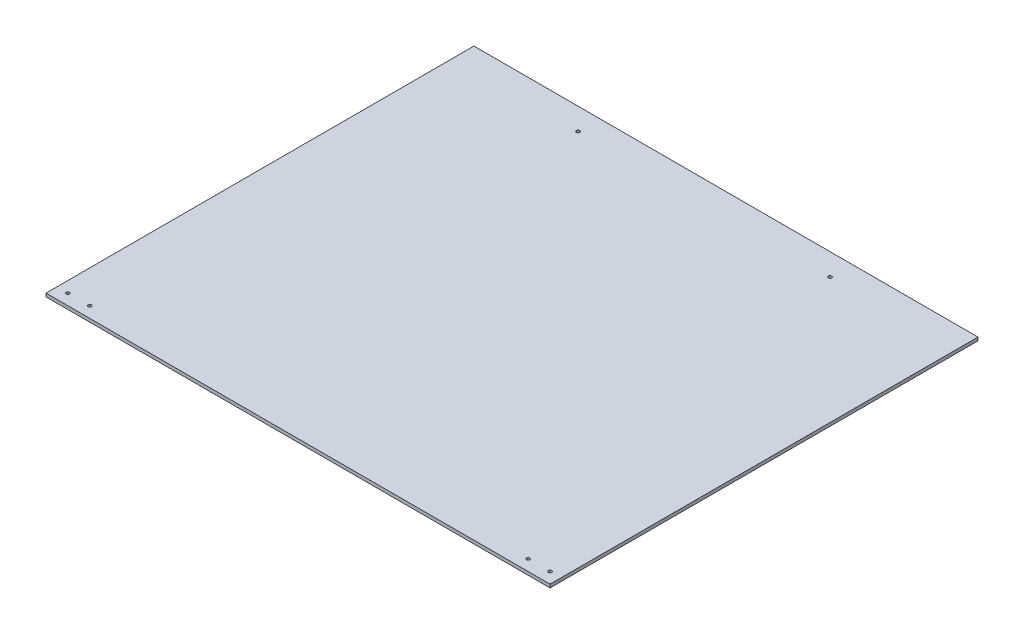
SolidWorks part; units mm, degrees
ref_plane "Front Plane" through (0, 0, 0) normal (0, 0, 1) x (1, 0, 0)
ref_plane "Top Plane" through (0, 0, 0) normal (0, 1, 0) x (1, 0, 0)
ref_plane "Right Plane" through (0, 0, 0) normal (1, 0, 0) x (0, 0, -1)
sketch "Sketch3" plane through (0, 0, 0) normal (0, 1, 0) x (1, 0, 0)
  line L0 (-190.2896, 141.7374) -> (-295.2896, 141.7374)
  line L1 (-295.2896, 141.7374) -> (-295.2896, -248.7941)
  line L2 (-295.2896, -248.7941) -> (164.7097, -248.7941)
  line L3 (164.7097, -248.7941) -> (164.7097, 141.7374)
  line L4 (-190.2896, 141.7374) -> (-170.2896, 141.7374)
  line L5 (-170.2896, 141.7374) -> (39.7104, 141.7374)
  line L6 (39.7104, 141.7374) -> (59.7104, 141.7374)
  line L7 (59.7104, 141.7374) -> (164.7097, 141.7374)
  circle A0 centre (-180.2896, 121.7374) radius 1.5
  circle A1 centre (49.7104, 121.7374) radius 1.5
extrude "Boss-Extrude2" add sketch "Sketch3" along normal blind 3
sketch "Sketch4" plane through (0, 3, 0) normal (0, 1, 0) x (1, 0, 0)
  circle A0 centre (134.7097, -238.7941) radius 1.5
  circle A1 centre (154.7097, -238.7941) radius 1.5
  circle A2 centre (-285.2896, -238.7941) radius 1.5
  circle A3 centre (-265.2896, -238.7941) radius 1.5
extrude "Cut-Extrude1" cut sketch "Sketch4" against normal blind 3
